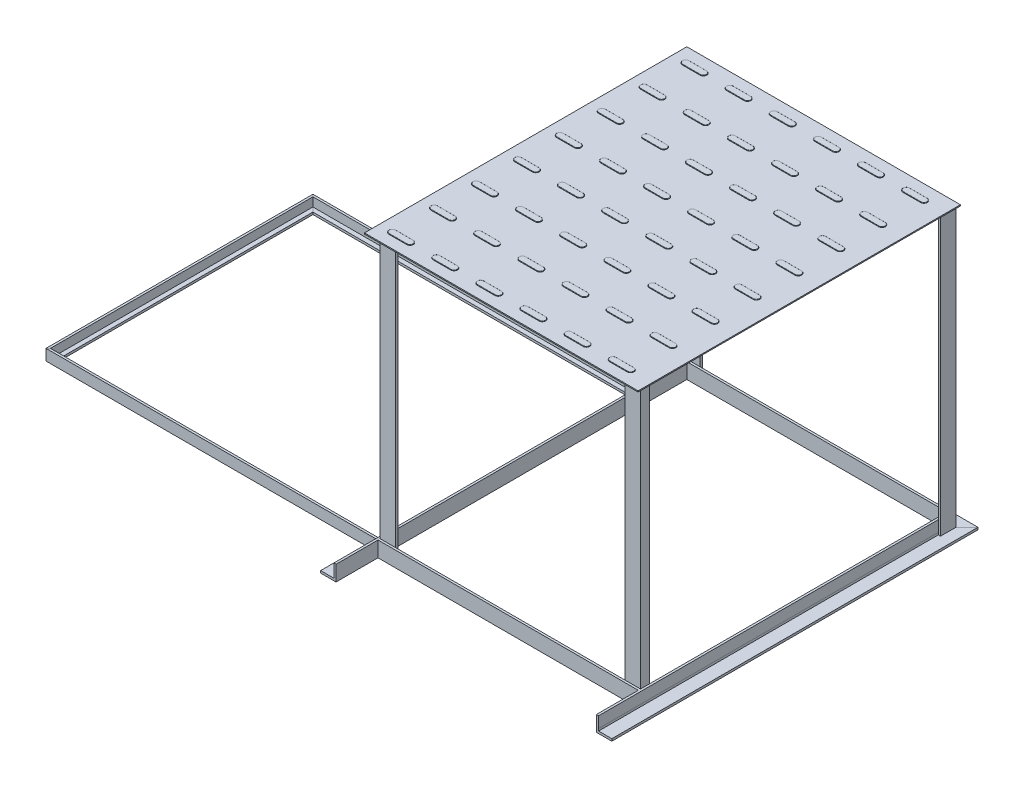
SolidWorks part; units mm, degrees
material "AISI 1010 Steel, hot rolled bar"
ref_plane "Front Plane" through (0, 0, 0) normal (0, 0, 1) x (1, 0, 0)
ref_plane "Top Plane" through (0, 0, 0) normal (0, 1, 0) x (1, 0, 0)
ref_plane "Right Plane" through (0, 0, 0) normal (1, 0, 0) x (0, 0, -1)
sketch "Sketch1" plane through (0, 0, 0) normal (0, 1, 0) x (1, 0, 0)
  line L0 (0, 0) -> (-150, 0)
  line L1 (-150, 0) -> (-150, -120)
  line L2 (-150, -120) -> (0, -120)
  dimension "D1" = 150
  dimension "D2" = 120
ref_plane "Plane1" through (0, 0, 0) normal (-1, 0, 0) x (0, 0, 1)
sketch "Sketch2" plane through (0, 0, 0) normal (-1, 0, 0) x (0, 0, 1)
  line L0 (0, 2.5) -> (0, -2.5) construction
  line L1 (-0.5, 2.5) -> (-0.5, -2.5)
  line L2 (0.5, 2.5) -> (0.5, -1.5)
  line L3 (-0.5, -2.5) -> (2.5, -2.5)
  line L4 (2.5, -2.5) -> (2.5, -1.5)
  line L5 (2.5, -1.5) -> (0.5, -1.5)
  line L6 (0.5, 2.5) -> (-0.5, 2.5)
  line L7 (-0.5, 2.5) -> (-0.5, -2.5) construction
  line L8 (0.5, 2.5) -> (0.5, -2.5) construction
  point P7 (0, 0)
  dimension "D1" = 5
  dimension "D4" = 3
  dimension "D5" = 1
  dimension "D6" = 2.5
  dimension "D2" = 0.5
  dimension "D3" = 0.5
sweep "Sweep1" add profiles "Sketch2" path "Sketch1"
sketch "Sketch5" plane through (0, 0, 0) normal (0, 1, 0) x (1, 0, 0)
  line L0 (0, -140.5) -> (0, 19.5)
  line L1 (0, 19.5) -> (120, 19.5)
  line L2 (120, 19.5) -> (120, -140.5)
  dimension "D1" = 0
  dimension "D2" = 120
  dimension "D3" = 160
  dimension "D4" = 20
ref_plane "Plane3" through (0, 0, 140.5) normal (0, 0, -1) x (-1, 0, 0)
sketch "Sketch6" plane through (0, 0, 140.5) normal (0, 0, -1) x (-1, 0, 0)
  line L0 (0, 3.5) -> (0, -1.5)
  line L2 (-1, 3.5) -> (-1, -3.5)
  line L4 (-1, -3.5) -> (6, -3.5)
  line L5 (6, -3.5) -> (6, -2.5)
  line L6 (150.5, -2.5) -> (0, -2.5) construction
  line L7 (6, -2.5) -> (0, -2.5)
  line L8 (-1, 3.5) -> (0, 3.5)
  line L9 (0, -2.5) -> (0, -1.5)
  point P5 (0, 0)
  dimension "D2" = 7
  dimension "D3" = 6
  dimension "D1" = 1
  dimension "D5" = 1
sweep "Sweep4" add profiles "Sketch6" path "Sketch5"
sketch "Sketch8" plane through (0, 0, 0) normal (1, 0, 0) x (0, 0, -1)
  line L0 (19.5, 3.5) -> (19.5, 123.5)
  dimension "D1" = 120
ref_plane "Plane4" through (120, 0, 0) normal (-1, 0, 0) x (0, 0, 1)
sketch "Sketch9" plane through (120, 0, 0) normal (-1, 0, 0) x (0, 0, 1)
  line L0 (-19.5, 3.5) -> (-19.5, 123.5)
ref_plane "Plane5" through (0, 123.5, -19.5) normal (0, 1, 0) x (1, 0, 0)
sketch "Sketch12" plane through (0, 123.5, -19.5) normal (0, 1, 0) x (1, 0, 0)
  line L0 (-1, 1) -> (-1, -6)
  line L2 (-1, -6) -> (0, -6)
  line L3 (0, -160) -> (0, 0) construction
  line L4 (-1, 1) -> (6, 1)
  line L5 (6, 1) -> (6, 0)
  line L6 (0, 0) -> (120, 0) construction
  line L7 (6, 0) -> (0, 0)
  line L8 (0, -6) -> (0, 0)
  dimension "D1" = 1
  dimension "D2" = 7
  dimension "D3" = 7
  dimension "D4" = 1
sweep "Sweep5" add profiles "Sketch12" path "Sketch8"
sketch "Sketch13" plane through (0, 3.5, 0) normal (0, -1, 0) x (1, 0, 0)
  line L6 (6, -19.5) -> (0, -19.5)
  line L7 (0, -19.5) -> (0, -13.5)
  line L8 (0, -19.5) -> (0, -13.5)
  line L9 (0, -13.5) -> (-1, -13.5)
  line L10 (-1, -20.5) -> (6, -20.5)
  line L11 (6, -20.5) -> (6, -19.5)
  line L12 (6, -19.5) -> (0, -19.5)
  line L13 (0, -13.5) -> (-1, -13.5)
  line L14 (-1, -13.5) -> (-1, -20.5)
  line L15 (-1, -13.5) -> (-1, -20.5)
  line L16 (-1, -20.5) -> (6, -20.5)
  line L17 (6, -20.5) -> (6, -19.5)
  dimension "D1" = 0
extrude "Boss-Extrude1" add sketch "Sketch13" along normal up to surface (6 mm away) up to face at (-3, -2.5, -11.5)
ref_plane "Plane6" through (120, 123.5, -19.5) normal (0, 1, 0) x (1, 0, 0)
sketch "Sketch14" plane through (120, 123.5, -19.5) normal (0, 1, 0) x (1, 0, 0)
  line L0 (0, 0) -> (0, -6)
  line L1 (0, 0) -> (0, -160) construction
  line L2 (0, -6) -> (1, -6)
  line L3 (1, -6) -> (1, 1)
  line L4 (1, 1) -> (-6, 1)
  line L5 (-6, 1) -> (-6, 0)
  line L6 (-114, 0) -> (0, 0) construction
  line L7 (-6, 0) -> (0, 0)
  dimension "D1" = 1
  dimension "D2" = 1
  dimension "D3" = 7
  dimension "D4" = 7
sweep "Sweep6" add profiles "Sketch14" path "Sketch9"
sketch "Sketch15" plane through (0, 3.5, 0) normal (0, -1, 0) x (1, 0, 0)
  line L6 (120, -19.5) -> (114, -19.5)
  line L7 (114, -19.5) -> (114, -20.5)
  line L8 (114, -20.5) -> (121, -20.5)
  line L9 (121, -20.5) -> (121, -13.5)
  line L10 (121, -13.5) -> (120, -13.5)
  line L11 (120, -13.5) -> (120, -19.5)
  line L12 (120, -19.5) -> (114, -19.5)
  line L13 (114, -19.5) -> (114, -20.5)
  line L14 (114, -20.5) -> (121, -20.5)
  line L15 (121, -20.5) -> (121, -13.5)
  line L16 (121, -13.5) -> (120, -13.5)
  line L17 (120, -13.5) -> (120, -19.5)
  dimension "D1" = 0
extrude "Boss-Extrude2" add sketch "Sketch15" along normal up to surface (6 mm away) up to face at (123, -2.5, 59)
ref_plane "Plane8" through (0, 0, 120.5) normal (0, 0, 1) x (1, 0, 0)
sketch "Sketch18" plane through (0, 0, 120.5) normal (0, 0, 1) x (1, 0, 0)
  line L0 (1, -2.5) -> (119, -2.5)
  line L1 (1, -3.5) -> (1, 3.5) construction
  line L2 (119, 3.5) -> (119, -3.5) construction
  dimension "D1" = 1
ref_plane "Plane9" through (119, -2.5, 120.5) normal (1, 0, 0) x (0, 0, -1)
sketch "Sketch19" plane through (119, -2.5, 120.5) normal (1, 0, 0) x (0, 0, -1)
  line L0 (-1, 6) -> (-1, -1)
  line L1 (146, -1) -> (-20, -1) construction
  line L2 (-1, -1) -> (4, -1)
  line L3 (4, -1) -> (4, 0)
  line L4 (4, 0) -> (0, 0)
  line L5 (0, 0) -> (0, 6)
  line L6 (0, 6) -> (-1, 6)
  point P8 (0.4939, 0)
  dimension "D1" = 7
  dimension "D3" = 5
  dimension "D4" = 1
sweep "Sweep7" add profiles "Sketch19" path "Sketch18"
sketch "Sketch20" plane through (0, 0, 120.5) normal (0, 0, -1) x (-1, 0, 0)
  line L0 (-1, 3.5) -> (-1, 123.5)
  dimension "D1" = 120
ref_plane "Plane10" through (1, 123.5, 120.5) normal (0, 1, 0) x (1, 0, 0)
sketch "Sketch21" plane through (1, 123.5, 120.5) normal (0, 1, 0) x (1, 0, 0)
  line L0 (0, 4) -> (0, 0)
  line L1 (0, 4) -> (0, 0) construction
  line L2 (0, 0) -> (0, 139) construction
  line L3 (0, 0) -> (7, 0)
  line L4 (0, 0) -> (118, 0) construction
  line L5 (7, 0) -> (7, 1)
  line L6 (7, 1) -> (1, 1)
  line L7 (1, 1) -> (1, 4)
  line L8 (0, 4) -> (118, 4) construction
  line L9 (1, 4) -> (0, 4)
  dimension "D1" = 1
  dimension "D2" = 1
  dimension "D3" = 7
sweep "Sweep8" add profiles "Sketch21" path "Sketch20"
sketch "Sketch22" plane through (0, 3.5, 0) normal (0, -1, 0) x (1, 0, 0)
  line L6 (1, 116.5) -> (2, 116.5)
  line L7 (2, 116.5) -> (2, 119.5)
  line L8 (2, 119.5) -> (8, 119.5)
  line L9 (8, 119.5) -> (8, 120.5)
  line L10 (8, 120.5) -> (1, 120.5)
  line L11 (1, 120.5) -> (1, 116.5)
  line L12 (1, 116.5) -> (2, 116.5)
  line L13 (2, 116.5) -> (2, 119.5)
  line L14 (2, 119.5) -> (8, 119.5)
  line L15 (8, 119.5) -> (8, 120.5)
  line L16 (8, 120.5) -> (1, 120.5)
  line L17 (1, 120.5) -> (1, 116.5)
  dimension "D1" = 0
extrude "Boss-Extrude3" add sketch "Sketch22" along normal up to surface (6 mm away) up to face at (60, -2.5, 118.5)
sketch "Sketch23" plane through (0, 0, 120.5) normal (0, 0, -1) x (-1, 0, 0)
  line L0 (-119, 3.5) -> (-119, 123.5)
  dimension "D1" = 120
ref_plane "Plane11" through (119, 123.5, 120.5) normal (0, 1, 0) x (1, 0, 0)
sketch "Sketch24" plane through (119, 123.5, 120.5) normal (0, 1, 0) x (1, 0, 0)
  line L0 (0, 4) -> (0, 0)
  line L1 (0, 0) -> (-7, 0)
  line L2 (-111, 0) -> (0, 0) construction
  line L3 (-7, 0) -> (-7, 1)
  line L4 (-7, 1) -> (-1, 1)
  line L5 (-1, 1) -> (-1, 4)
  line L6 (-117, 4) -> (0, 4) construction
  line L7 (-1, 4) -> (0, 4)
  dimension "D1" = 7
  dimension "D2" = 1
  dimension "D3" = 1
sweep "Sweep9" add profiles "Sketch24" path "Sketch23"
sketch "Sketch25" plane through (0, 3.5, 0) normal (0, -1, 0) x (1, 0, 0)
  line L6 (118, 116.5) -> (119, 116.5)
  line L7 (119, 116.5) -> (119, 120.5)
  line L8 (119, 120.5) -> (112, 120.5)
  line L9 (112, 120.5) -> (112, 119.5)
  line L10 (112, 119.5) -> (118, 119.5)
  line L11 (118, 119.5) -> (118, 116.5)
  line L12 (118, 116.5) -> (119, 116.5)
  line L13 (119, 116.5) -> (119, 120.5)
  line L14 (119, 120.5) -> (112, 120.5)
  line L15 (112, 120.5) -> (112, 119.5)
  line L16 (112, 119.5) -> (118, 119.5)
  line L17 (118, 119.5) -> (118, 116.5)
  dimension "D1" = 0
extrude "Boss-Extrude4" add sketch "Sketch25" along normal up to surface (6 mm away) up to face at (43, -2.5, 118.8333)
sketch "Sketch26" plane through (0, 123.5, 0) normal (0, 1, 0) x (1, 0, 0)
  line L0 (-1, 20.5) -> (-6, 25.5) construction
  line L1 (-2.1467, 21.6467) -> (121.8884, 21.6467)
  line L2 (-2.1467, 21.6467) -> (-2.1467, -124.4703)
  line L3 (-2.1467, -124.4703) -> (121.8884, -124.4703)
  line L4 (121.8884, 21.6467) -> (121.8884, -124.4703)
extrude "Boss-Extrude5" add sketch "Sketch26" along normal blind 0.5
sketch "Sketch27" plane through (0, 124, 0) normal (0, 1, 0) x (1, 0, 0)
  line L0 (4, 15) -> (12, 15) construction
  line L1 (4, 16.5) -> (12, 16.5)
  line L2 (4, 13.5) -> (12, 13.5)
  arc A0 (4, 16.5) -> (4, 13.5) centre (4, 15) ccw
  arc A1 (12, 13.5) -> (12, 16.5) centre (12, 15) ccw
  point P2 (8, 15)
  dimension "D3" = 1.5
  dimension "D1" = 15
  dimension "D2" = 8
  dimension "D4" = 8
extrude "Boss-Extrude6" add sketch "Sketch27" along normal blind 0.25
fillet "Fillet1" radius 0.125 4 edges at (8, 124.25, -16.5) (13.5, 124.25, -15) (8, 124.25, -13.5) (2.5, 124.25, -15)
fillet "Fillet2" radius 0.025 4 edges at (2.5, 124, -15) (8, 124, -16.5) (13.5, 124, -15) (8, 124, -13.5)
pattern_linear "LPattern2" count 8 spacing 19 along (0, 0, 1) count 6 spacing 20 along (1, 0, 0) of "Fillet2", "Fillet1", "Boss-Extrude6"
